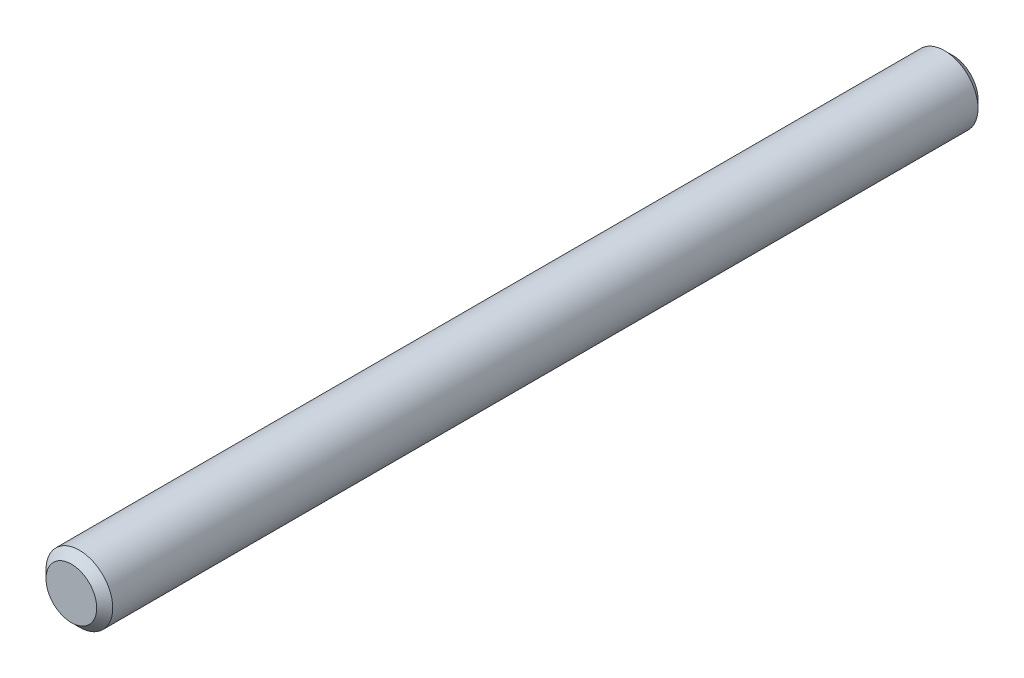
SolidWorks part; units mm, degrees
ref_plane "Front Plane" through (0, 0, 0) normal (0, 0, 1) x (1, 0, 0)
ref_plane "Top Plane" through (0, 0, 0) normal (0, 1, 0) x (1, 0, 0)
ref_plane "Right Plane" through (0, 0, 0) normal (1, 0, 0) x (0, 0, -1)
sketch "Sketch1" plane through (0, 0, 0) normal (0, 0, 1) x (1, 0, 0)
  circle A0 centre (0, 0) radius 12.5
extrude "Boss-Extrude1" add sketch "Sketch1" along normal mid plane 330
chamfer "Chamfer1" distance 3 angle 45 2 edges at (12.5, 0, -165) (12.5, 0, 165)
